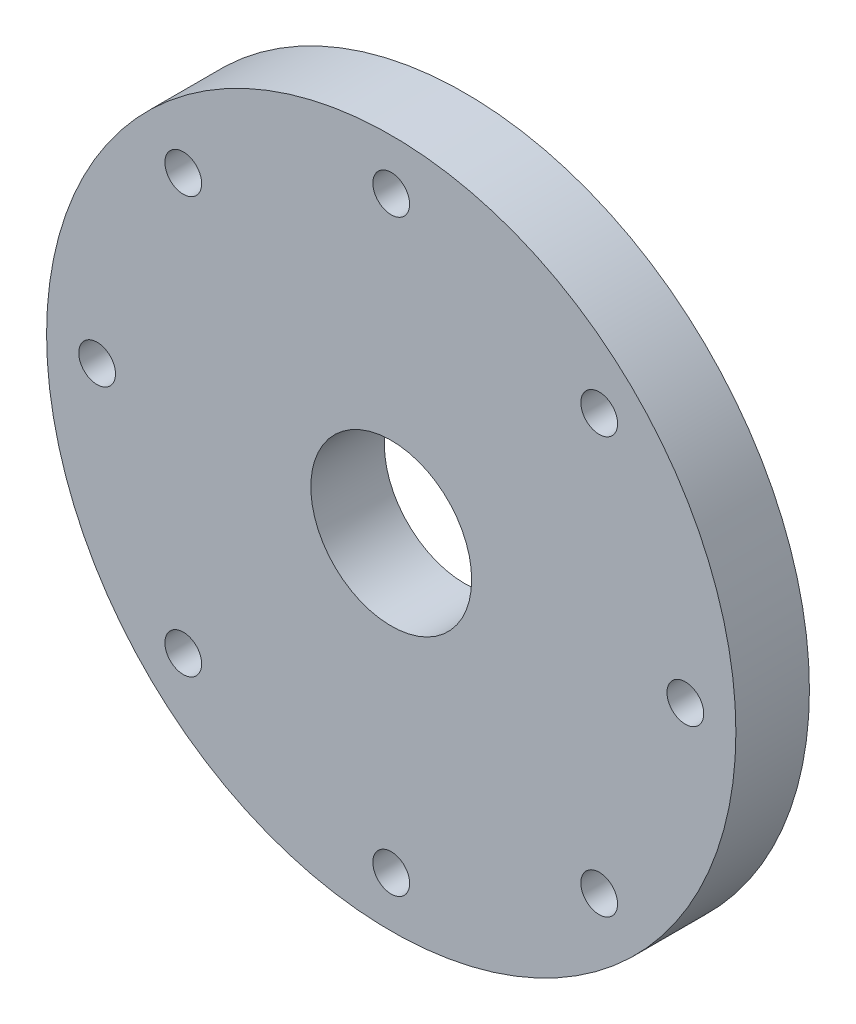
SolidWorks part; units mm, degrees
ref_plane "Front Plane" through (0, 0, 0) normal (0, 0, 1) x (1, 0, 0)
ref_plane "Top Plane" through (0, 0, 0) normal (0, 1, 0) x (1, 0, 0)
ref_plane "Right Plane" through (0, 0, 0) normal (1, 0, 0) x (0, 0, -1)
sketch "Sketch1" plane through (0, 0, 0) normal (0, 1, 0) x (1, 0, 0)
  line L0 (75, -14) -> (0, -14)
  line L1 (0, -14) -> (0, -30)
  line L2 (0, -30) -> (75, -30)
  line L3 (75, -30) -> (75, -14)
  line L4 (0, -14) -> (0, -30) construction
  dimension "D1" = 16
  dimension "D2" = 75
revolve "Revolve1" add sketch "Sketch1" angle 360 about L4
hole_wizard "Ø8.0 (8) Diameter Hole1" positions "Sketch5" profile "Sketch4" hole size "Ø8.0" standard "ANSI Metric"
sketch "Sketch5" plane through (0, 0, 14) normal (0, 0, -1) x (-1, 0, 0)
  point P0 (45.2548, 45.2548)
  point P1 (-45.2548, 45.2548)
  point P2 (-45.2548, -45.2548)
  point P3 (45.2548, -45.2548)
sketch "Sketch4" plane through (-45.2548, 45.2548, 14) normal (1, 0, 0) x (0, 1, 0)
  line L0 (0, 0) -> (0, 32.4034)
  line L1 (0, 32.4034) -> (4, 30)
  line L2 (4, 30) -> (4, 0)
  line L5 (4, 0) -> (0, 0)
  line L10 (0, 32.4034) -> (-4, 30) construction
  line L11 (0, -6.35) -> (0, 107.95) construction
  dimension "Hole Dia." = 8
  dimension "Hole Depth" = 30
  dimension "Drill Angle" = 118
hole_wizard "M6 Clearance Hole1" positions "Sketch7" profile "Sketch6" hole size "M6" standard "ANSI Metric"
sketch "Sketch7" plane through (0, 0, 30) normal (0, 0, 1) x (1, 0, 0)
  point P0 (0, 64)
  point P1 (0, -64)
  point P2 (64, 0)
  point P3 (-64, 0)
sketch "Sketch6" plane through (0, 64, 30) normal (1, 0, 0) x (0, -1, 0)
  line L0 (0, 0) -> (0, 24.4034)
  line L1 (0, 24.4034) -> (4, 22)
  line L2 (4, 22) -> (4, 0)
  line L5 (4, 0) -> (0, 0)
  line L10 (0, 24.4034) -> (-4, 22) construction
  line L11 (0, -6.35) -> (0, 107.95) construction
  dimension "Hole Dia." = 8
  dimension "Hole Depth" = 22
  dimension "Drill Angle" = 118
sketch "Sketch8" plane through (0, 0, 30) normal (0, 0, 1) x (1, 0, 0)
  circle A0 centre (0, 0) radius 17.5
extrude "Cut-Extrude1" cut sketch "Sketch8" against normal blind 30
